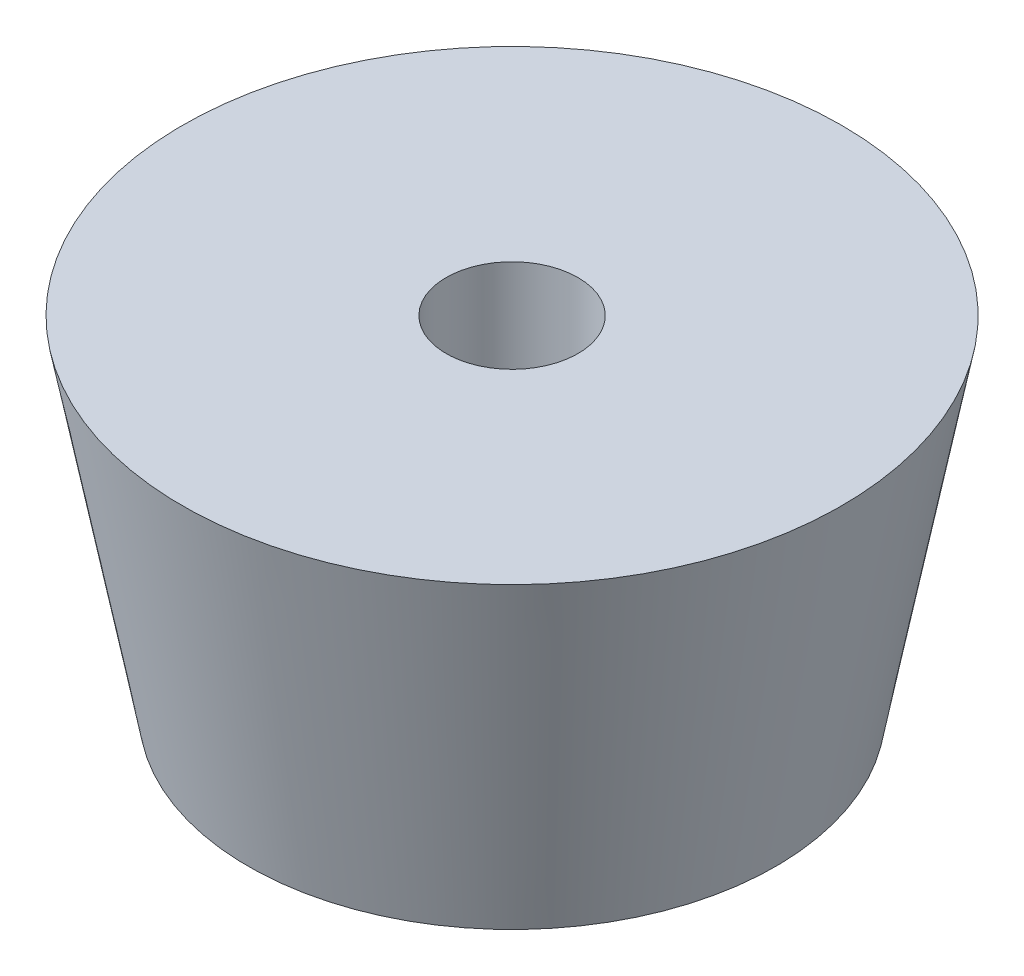
SolidWorks part; units mm, degrees
ref_plane "Front Plane" through (0, 0, 0) normal (0, 0, 1) x (1, 0, 0)
ref_plane "Top Plane" through (0, 0, 0) normal (0, 1, 0) x (1, 0, 0)
ref_plane "Right Plane" through (0, 0, 0) normal (1, 0, 0) x (0, 0, -1)
sketch "Sketch2" plane through (0, 0, 0) normal (0, 0, 1) x (1, 0, 0)
  line L0 (0, 0) -> (6, 0)
  line L1 (0, 0) -> (0, 39.6896) construction
  line L2 (0, 7.8581) -> (7.5, 7.8581)
  line L3 (6, 0) -> (7.5, 7.8581)
  line L4 (0, 0) -> (0, 7.8581)
  dimension "D1" = 7.5
  dimension "D2" = 8
  dimension "D3" = 6
revolve "Revolve1" add sketch "Sketch2" angle 360 about L1
sketch "Sketch3" plane through (0, 0, 0) normal (0, -1, 0) x (-1, 0, 0)
  circle A0 centre (0, 0) radius 1.5
extrude "Cut-Extrude1" cut sketch "Sketch3" against normal through all
sketch "Sketch4" plane through (0, 0, 0) normal (0, -1, 0) x (-1, 0, 0)
  circle A0 centre (0, 0) radius 3.5
extrude "Cut-Extrude2" cut sketch "Sketch4" against normal blind 5
